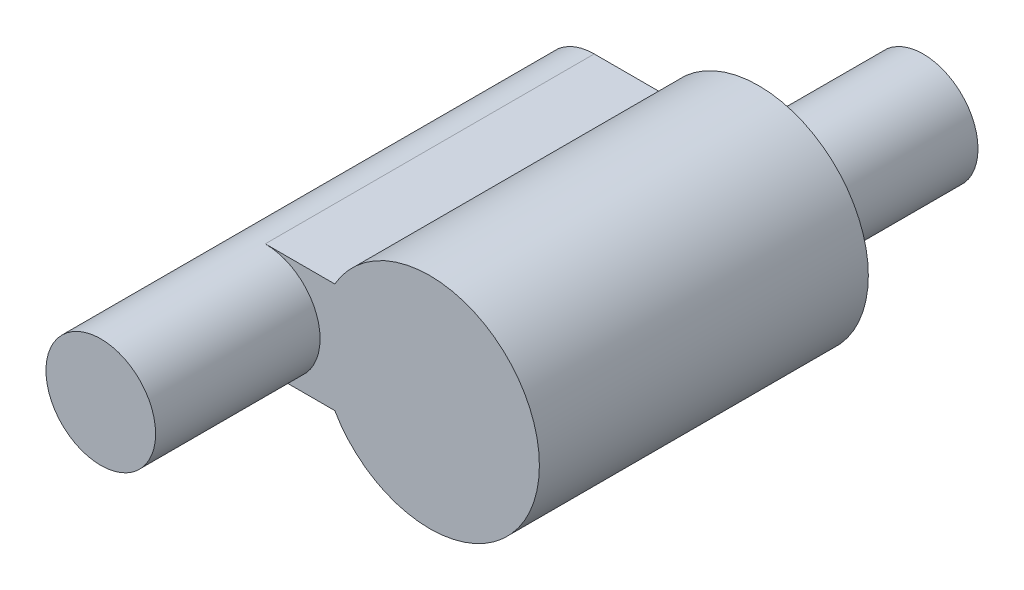
SolidWorks part; units mm, degrees
ref_plane "Спереди" through (0, 0, 0) normal (0, 0, 1) x (1, 0, 0)
ref_plane "Сверху" through (0, 0, 0) normal (0, 1, 0) x (1, 0, 0)
ref_plane "Справа" through (0, 0, 0) normal (1, 0, 0) x (0, 0, -1)
other "Configuration Table"
sketch "Sketch1" plane through (0, 0, 0) normal (0, 0, 1) x (1, 0, 0)
  line L0 (-8.1564, 7.0316) -> (3.7864, 7.0316) construction
  line L1 (-7.068, 8.0316) -> (-5.8001, 8.0316)
  line L5 (-7.068, 6.0316) -> (-5.8001, 6.0316)
  arc A2 (-7.068, 8.0316) -> (-7.068, 6.0316) centre (-7.068, 7.0316) ccw
  arc A3 (-5.8001, 6.0316) -> (-5.8001, 8.0316) centre (-4.068, 7.0316) ccw
  arc A4 (-5.8001, 6.0316) -> (-6.068, 7.0316) centre (-4.068, 7.0316) cw construction
  arc A5 (-6.068, 7.0316) -> (-5.668, 8.2316) centre (-4.068, 7.0316) cw construction
  arc A6 (-7.068, 6.0316) -> (-6.068, 7.0316) centre (-7.068, 7.0316) ccw construction
  arc A7 (-6.068, 7.0316) -> (-7.068, 8.0316) centre (-7.068, 7.0316) ccw construction
  dimension "D1" = 4
  dimension "D4" = 2
  dimension "D3" = 3
  dimension "D2" = 2
extrude "Boss-Extrude1" add sketch "Sketch1" along normal blind 6
ref_plane "Plane1" through (0, 0, 6) normal (0, 0, 1) x (1, 0, 0)
sketch "Sketch2" plane through (0, 0, 6) normal (0, 0, 1) x (1, 0, 0)
  arc A3 (-7.068, 8.0316) -> (-7.068, 6.0316) centre (-7.068, 7.0316) ccw construction
  circle A4 centre (-7.068, 7.0316) radius 1
  point P4 (-8.068, 7.0316)
extrude "Boss-Extrude2" add sketch "Sketch2" along normal blind 3
ref_plane "Plane2" through (0, 0, 0) normal (0, 0, -1) x (-1, 0, 0)
sketch "Sketch3" plane through (0, 0, 0) normal (0, 0, -1) x (-1, 0, 0)
  circle A2 centre (4.068, 7.0316) radius 1
  arc A3 (7.068, 8.0316) -> (7.068, 6.0316) centre (7.068, 7.0316) ccw construction
extrude "Boss-Extrude3" add sketch "Sketch3" along normal blind 3
equation "\"R small\"= 2"
equation "\"R big\"= 4"
equation "\"width\"= 0.6"
equation "\"border width\"= 1"
equation "\"D2@Sketch1\"=\"R small\""
equation "\"D4@Sketch1\"=\"R small\""
equation "\"D1@Sketch1\"=\"R big\""
